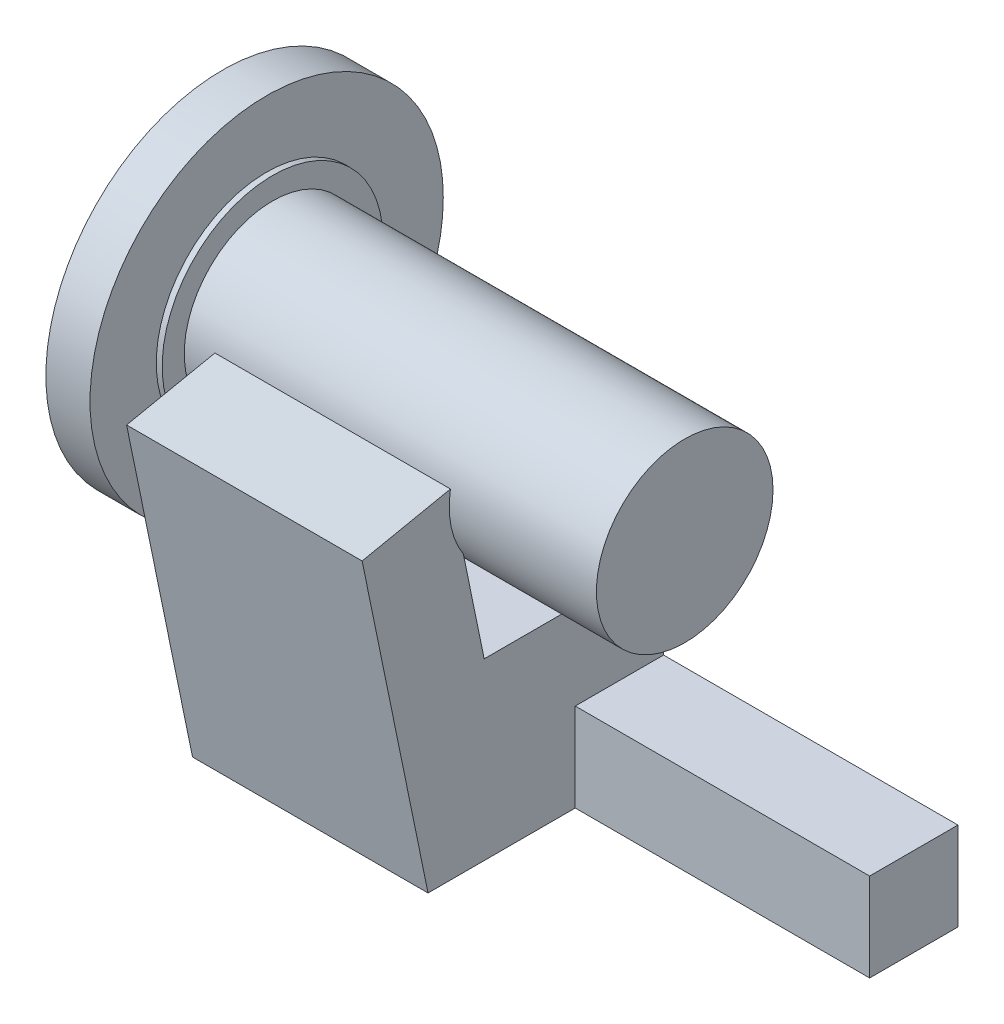
SolidWorks part; units mm, degrees
ref_plane "Front Plane" through (0, 0, 0) normal (0, 0, 1) x (1, 0, 0)
ref_plane "Top Plane" through (0, 0, 0) normal (0, 1, 0) x (1, 0, 0)
ref_plane "Right Plane" through (0, 0, 0) normal (1, 0, 0) x (0, 0, -1)
sketch "Sketch1" plane through (0, 0, 0) normal (1, 0, 0) x (0, 0, -1)
  circle A0 centre (0, 0) radius 76.2
  dimension "D1" = 152.4
extrude "Boss-Extrude1" add sketch "Sketch1" along normal blind 19.05
sketch "Sketch2" plane through (19.05, 0, 0) normal (1, 0, 0) x (0, 0, -1)
  circle A0 centre (0, 0) radius 47.625
  dimension "D1" = 95.25
extrude "Boss-Extrude2" add sketch "Sketch2" along normal blind 2.54
sketch "Sketch3" plane through (21.59, 0, 0) normal (1, 0, 0) x (0, 0, -1)
  circle A0 centre (0, 0) radius 38.1
  dimension "D1" = 76.2
extrude "Boss-Extrude3" add sketch "Sketch3" along normal blind 177.8
sketch "Sketch4" plane through (0, 0, 0) normal (-1, 0, 0) x (0, 0, 1)
  circle A0 centre (0, 0) radius 12.7
  dimension "D1" = 25.4
extrude "Boss-Extrude4" add sketch "Sketch4" along normal blind 31.75
ref_plane "Plane1" through (34.29, 0, 0) normal (1, 0, 0) x (0, 0, -1)
sketch "Sketch7" plane through (34.29, 0, 0) normal (1, 0, 0) x (0, 0, -1)
  line L0 (-37.5561, 6.415) -> (-75.6561, -1.42)
  line L2 (-75.6561, -1.42) -> (-47.2197, -139.7)
  line L4 (-47.2197, -139.7) -> (54.3803, -139.7)
  line L5 (54.3803, -139.7) -> (54.3803, -109.3673)
  line L8 (-23.0085, -64.3268) -> (31.7291, -64.3268)
  line L9 (54.3803, -87.2809) -> (54.3803, -109.3673)
  line L10 (-37.5561, 6.415) -> (-23.0085, -64.3268)
  line L11 (-38.1, 0) -> (-38.1, -139.7) construction
  line L12 (83.82, 0) -> (-83.82, 0) construction
  circle A0 centre (0, 0) radius 38.1 construction
  arc A1 (31.7291, -64.3268) -> (54.3803, -87.2809) centre (31.8863, -86.8249) cw
  dimension "D1" = 38.1
  dimension "D2" = 101.6
  dimension "D3" = 139.7
extrude "Boss-Extrude5" add sketch "Sketch7" along normal blind 101.6
sketch "Sketch8" plane through (135.89, 0, 0) normal (1, 0, 0) x (0, 0, -1)
  line L0 (0, 118.745) -> (0, -118.745) construction
  line L6 (54.3803, -139.7) -> (16.2803, -139.7)
  line L8 (54.3803, -139.7) -> (54.3803, -101.6)
  line L9 (54.3803, -101.6) -> (16.2803, -101.6)
  line L10 (16.2803, -139.7) -> (16.2803, -101.6)
  point P0 (0, -120.65)
  dimension "D1" = 38.1
  dimension "D2" = 38.1
extrude "Boss-Extrude6" add sketch "Sketch8" along normal blind 127
sketch "Sketch9" plane through (0, -139.7, 0) normal (0, -1, 0) x (-1, 0, 0)
  line L4 (-262.89, 54.3803) -> (-34.29, 54.3803) construction
  line L5 (-34.29, -47.2197) -> (-34.29, 54.3803) construction
  circle A1 centre (-40.64, 48.0303) radius 6.35
  point P6 (-53.0969, 75.7246)
  dimension "D1" = 12.7
  dimension "D2" = 6.35
  dimension "D3" = 6.35
extrude "Boss-Extrude7" add sketch "Sketch9" along normal blind 2.54
